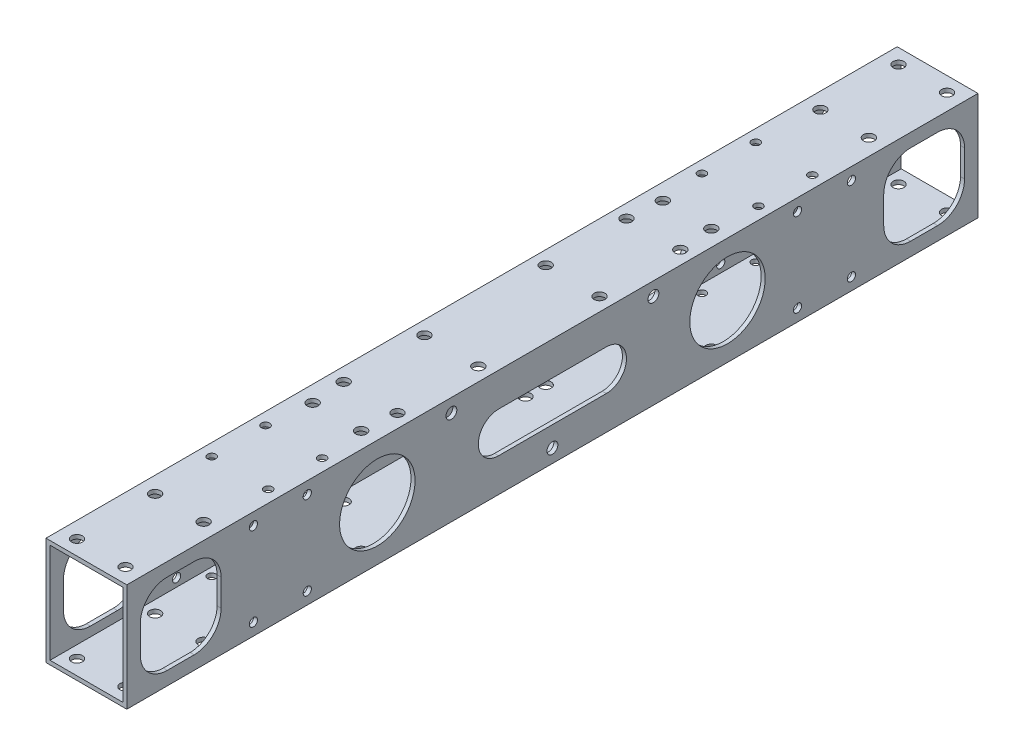
SolidWorks part; units mm, degrees
material "1060 合金"
ref_plane "前视基准面" through (0, 0, 0) normal (0, 0, 1) x (1, 0, 0)
ref_plane "上视基准面" through (0, 0, 0) normal (0, 1, 0) x (1, 0, 0)
ref_plane "右视基准面" through (0, 0, 0) normal (1, 0, 0) x (0, 0, -1)
other "Configuration Table"
sketch "草图1" plane through (0, 0, 0) normal (0, 0, 1) x (1, 0, 0)
  line L0 (-15, -20) -> (-15, 20)
  line L1 (-13.5, -18.5) -> (13.5, -18.5)
  line L2 (-13.5, -18.5) -> (-13.5, 18.5)
  line L3 (-13.5, 18.5) -> (13.5, 18.5)
  line L4 (13.5, -18.5) -> (13.5, 18.5)
  line L5 (-13.5, -18.5) -> (13.5, 18.5) construction
  line L6 (-13.5, 18.5) -> (13.5, -18.5) construction
  line L7 (-15, 20) -> (15, 20)
  line L8 (15, -20) -> (15, 20)
  line L9 (-15, -20) -> (15, -20)
  point P0 (0, 0)
  dimension "D2" = 30
  dimension "D3" = 40
  dimension "D1" = 1.5
extrude "凸台-拉伸1" add sketch "草图1" along normal mid plane 316
sketch "草图2" plane through (15, 0, 0) normal (1, 0, 0) x (0, 0, -1)
  line L0 (0, 0) -> (50000, 0) construction
  line L1 (-158, -20) -> (158, -20) construction
  line L2 (-158, 20) -> (-118, 20) construction
  line L3 (-158, 20) -> (-158, -20) construction
  line L4 (-158, -20) -> (-118, -20) construction
  line L5 (-118, 20) -> (-118, -20) construction
  line L6 (-158, 20) -> (-118, -20) construction
  line L7 (0, 0) -> (0, -50000) construction
  line L8 (-153, -15) -> (-123, -15)
  line L9 (-153, -15) -> (-153, 15)
  line L10 (-153, 15) -> (-123, 15)
  line L11 (-123, -15) -> (-123, 15)
  line L12 (-153, -15) -> (-123, 15) construction
  line L13 (-153, 15) -> (-123, -15) construction
  line L14 (153, 15) -> (123, 15)
  line L15 (123, -15) -> (123, 15)
  line L16 (153, -15) -> (123, -15)
  line L17 (153, -15) -> (153, 15)
  line L18 (-20, 0) -> (20, 0) construction
  line L19 (-20, 7.5) -> (20, 7.5)
  line L20 (-20, -7.5) -> (20, -7.5)
  line L21 (-65, 0) -> (65, 0) construction
  arc A1 (-20, 7.5) -> (-20, -7.5) centre (-20, 0) ccw
  arc A2 (20, -7.5) -> (20, 7.5) centre (20, 0) ccw
  circle A3 centre (-65, 0) radius 14
  circle A4 centre (65, 0) radius 14
  point P10 (-138, 0)
  point P23 (0, 0)
  point P31 (0, 0)
  dimension "D2" = 30
  dimension "D6" = 28
  dimension "D1" = 40
  dimension "D3" = 15
  dimension "D4" = 40
  dimension "D5" = 130
extrude "切除-拉伸1" cut sketch "草图2" against normal blind 50
fillet "圆角1" radius 10 16 edges at (14.25, 15, -153) (-14.25, 15, -153) (14.25, 15, -123) (-14.25, 15, -123) (14.25, -15, -123) (-14.25, -15, -123) (-14.25, -15, -153) (14.25, 15, 123) (-14.25, 15, 123) (14.25, 15, 153) (-14.25, 15, 153) (14.25, -15, 153) (-14.25, -15, 153) (14.25, -15, 123) (-14.25, -15, 123) (14.25, -15, -153)
sketch "草图3" plane through (0, 20, 0) normal (0, 1, 0) x (1, 0, 0)
  line L0 (0, 0) -> (15, 0) construction
  line L1 (100, -45) -> (10, -45) construction
  line L2 (100, -45) -> (100, 45) construction
  line L3 (100, 45) -> (10, 45) construction
  line L4 (10, -45) -> (10, 45) construction
  line L5 (100, -45) -> (10, 45) construction
  line L6 (100, 45) -> (10, -45) construction
  line L7 (15, -158) -> (15, 158) construction
  line L8 (15, 0) -> (55, 0) construction
  circle A0 centre (10, 45) radius 2.5
  circle A1 centre (10, -45) radius 2.5
  point P0 (55, 0)
  dimension "D3" = 5
  dimension "D1" = 90
  dimension "D2" = 40
sketch "草图4" plane through (0, 20, 0) normal (0, 1, 0) x (1, 0, 0)
  line L0 (0, 0) -> (0, -50000) construction
  line L1 (-9, 65) -> (9, 65) construction
  line L2 (-9, 123.5) -> (9, 123.5) construction
  line L3 (-9, 123.5) -> (-9, 152.5) construction
  line L4 (-9, 152.5) -> (9, 152.5) construction
  line L5 (9, 123.5) -> (9, 152.5) construction
  line L6 (-9, 123.5) -> (9, 152.5) construction
  line L7 (-9, 152.5) -> (9, 123.5) construction
  line L8 (15, 158) -> (-15, 158) construction
  circle A0 centre (-9, 152.5) radius 2.025
  circle A1 centre (9, 152.5) radius 2.025
  circle A2 centre (-9, 123.5) radius 2.025
  circle A3 centre (9, 123.5) radius 2.025
  circle A4 centre (-9, 65) radius 2.025
  circle A5 centre (9, 65) radius 2.025
  point P3 (0, 138)
  point P11 (0, 65)
  dimension "D5" = 4.05
  dimension "D1" = 18
  dimension "D2" = 138
  dimension "D3" = 29
  dimension "D4" = 93
extrude "切除-拉伸2" cut sketch "草图4" against normal blind 40
mirror "镜向1" about plane through (0, 0, 0) normal (0, 0, 1) of "切除-拉伸2"
sketch "草图5" plane through (0, 20, 0) normal (0, 1, 0) x (1, 0, 0)
  line L0 (15, 0) -> (65, 0) construction
  line L1 (15, -158) -> (15, 158) construction
  line L2 (0, 0) -> (0, -50000) construction
  line L3 (120, -52.5) -> (10, -52.5) construction
  line L4 (120, -52.5) -> (120, 52.5) construction
  line L5 (120, 52.5) -> (10, 52.5) construction
  line L6 (10, -52.5) -> (10, 52.5) construction
  line L7 (120, -52.5) -> (10, 52.5) construction
  line L8 (120, 52.5) -> (10, -52.5) construction
  line L9 (-120, 52.5) -> (-10, -52.5) construction
  line L10 (-120, -52.5) -> (-10, 52.5) construction
  line L11 (-10, -52.5) -> (-10, 52.5) construction
  line L12 (-120, 52.5) -> (-10, 52.5) construction
  line L13 (-120, -52.5) -> (-120, 52.5) construction
  line L14 (-120, -52.5) -> (-10, -52.5) construction
  line L15 (-15, 0) -> (-65, 0) construction
  circle A0 centre (10, 52.5) radius 2.025
  circle A1 centre (10, -52.5) radius 2.025
  circle A3 centre (-10, -52.5) radius 2.025
  circle A4 centre (-10, 52.5) radius 2.025
  dimension "D3" = 4.05
  dimension "D4" = 105
  dimension "D1" = 50
  dimension "D2" = 110
extrude "切除-拉伸3" cut sketch "草图5" against normal blind 50
sketch "草图7" plane through (15, 0, 0) normal (1, 0, 0) x (0, 0, -1)
  line L0 (-37.5, 15) -> (37.5, 15) construction
  line L1 (0, 0) -> (0, 15) construction
  line L2 (-158, 20) -> (158, 20) construction
  circle A0 centre (-37.5, 15) radius 2.025
  circle A1 centre (37.5, 15) radius 2.025
  dimension "D1" = 5
  dimension "D3" = 4.05
  dimension "D2" = 75
extrude "切除-拉伸4" cut sketch "草图7" against normal blind 47
sketch "草图8" plane through (15, 0, 0) normal (1, 0, 0) x (0, 0, -1)
  line L0 (0, 0) -> (0, -15) construction
  line L1 (-158, -20) -> (158, -20) construction
  circle A0 centre (0, -15) radius 2.025
  dimension "D1" = 5
  dimension "D2" = 4.05
extrude "切除-拉伸5" cut sketch "草图8" against normal blind 67
sketch "草图9" plane through (0, -20, 0) normal (0, -1, 0) x (1, 0, 0)
  line L0 (0, 0) -> (10, 0) construction
  line L1 (10, 15) -> (10, -15) construction
  line L2 (15, 158) -> (15, -158) construction
  line L3 (0, 0) -> (0, -50000) construction
  circle A0 centre (10, 15) radius 2.025
  circle A1 centre (10, -15) radius 2.025
  circle A2 centre (-10, -15) radius 2.025
  circle A3 centre (-10, 15) radius 2.025
  point P6 (10, 0)
  dimension "D1" = 4.05
  dimension "D2" = 5
  dimension "D3" = 30
extrude "切除-拉伸6" cut sketch "草图9" against normal blind 27
sketch "草图10" plane through (15, 0, 0) normal (1, 0, 0) x (0, 0, -1)
  line L0 (91, 15.5) -> (111, 15.5) construction
  line L1 (-158, 20) -> (158, 20) construction
  line L2 (79, 0) -> (123, 0) construction
  line L3 (123, 5) -> (123, -5) construction
  line L4 (101, 15.5) -> (101, 0) construction
  circle A0 centre (91, 15.5) radius 1.525
  circle A1 centre (111, 15.5) radius 1.525
  circle A2 centre (65, 0) radius 14 construction
  dimension "D2" = 3.05
  dimension "D1" = 4.5
  dimension "D3" = 20
extrude "切除-拉伸7" cut sketch "草图10" against normal blind 10
sketch "草图11" plane through (0, 20, 0) normal (0, 1, 0) x (1, 0, 0)
  line L0 (10.5, 101) -> (10.5, 81) construction
  line L1 (15, -158) -> (15, 158) construction
  line L3 (15, 158) -> (-15, 158) construction
  circle A0 centre (10.5, 101) radius 1.525
  circle A1 centre (10.5, 81) radius 1.525
  dimension "D2" = 3.05
  dimension "D4" = 57
  dimension "D1" = 4.5
  dimension "D3" = 20
extrude "切除-拉伸8" cut sketch "草图11" against normal blind 10
mirror "镜向2" about plane through (0, 0, 0) normal (0, 0, 1) of "切除-拉伸7", "切除-拉伸8"
mirror "镜向3" about plane through (0, 0, 0) normal (0, 1, 0) of "镜向2", "切除-拉伸7", "切除-拉伸8"
mirror "镜向4" about plane through (0, 0, 0) normal (1, 0, 0) of "镜向3", "切除-拉伸7", "切除-拉伸8", "镜向2"
sketch "草图12" plane through (0, 20, 0) normal (0, 1, 0) x (1, 0, 0)
  line L0 (10, 22.5) -> (10, 52.5) construction
  line L1 (-10, -22.5) -> (10, -22.5) construction
  line L2 (-10, -22.5) -> (-10, 22.5) construction
  line L3 (-10, 22.5) -> (10, 22.5) construction
  line L4 (10, -22.5) -> (10, 22.5) construction
  line L5 (-10, -22.5) -> (10, 22.5) construction
  line L6 (-10, 22.5) -> (10, -22.5) construction
  circle A0 centre (-10, 22.5) radius 2.025
  circle A1 centre (10, 22.5) radius 2.025
  circle A2 centre (-10, -22.5) radius 2.025
  circle A3 centre (10, -22.5) radius 2.025
  circle A4 centre (-10, 52.5) radius 2.025 construction
  point P0 (0, 0)
  dimension "D1" = 30
extrude "切除-拉伸9" cut sketch "草图12" against normal blind 60
